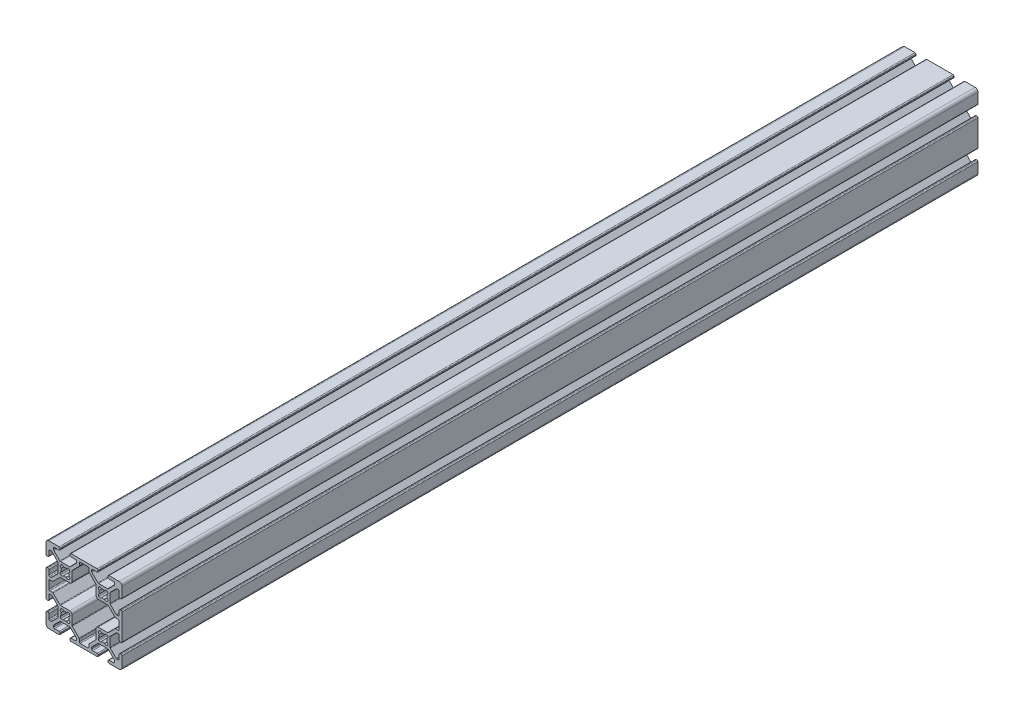
SolidWorks part; units mm, degrees
ref_plane "Front Plane" through (0, 0, 0) normal (0, 0, 1) x (1, 0, 0)
ref_plane "Top Plane" through (0, 0, 0) normal (0, 1, 0) x (1, 0, 0)
ref_plane "Right Plane" through (0, 0, 0) normal (1, 0, 0) x (0, 0, -1)
ref_plane "Plane1" through (0, 0, -450) normal (0, 0, -1) x (-1, 0, 0)
sketch "Sketch1" plane through (0, 0, -450) normal (0, 0, -1) x (-1, 0, 0)
  line L0 (18.5, 11.997) -> (18.5, 8.003)
  line L1 (17.992, 7.495) -> (16.6449, 7.495)
  line L2 (16.2857, 7.3462) -> (12.7433, 3.8038)
  line L3 (12.3841, 3.655) -> (7.488, 3.655)
  line L4 (6.345, 2.512) -> (6.345, -2.3838)
  line L5 (6.1962, -2.743) -> (2.6538, -6.2854)
  line L6 (2.505, -6.6446) -> (2.505, -7.992)
  line L7 (1.997, -8.5) -> (-1.997, -8.5)
  line L8 (-2.505, -7.992) -> (-2.505, -6.6446)
  line L9 (-2.6538, -6.2854) -> (-6.1962, -2.743)
  line L10 (-6.345, -2.3838) -> (-6.345, 2.512)
  line L11 (-7.488, 3.655) -> (-12.3841, 3.655)
  line L12 (-12.7433, 3.8038) -> (-16.2857, 7.3462)
  line L13 (-16.6449, 7.495) -> (-17.992, 7.495)
  line L14 (-18.5, 8.003) -> (-18.5, 11.997)
  line L15 (-17.992, 12.505) -> (-16.6449, 12.505)
  line L16 (-16.2857, 12.6538) -> (-12.7433, 16.1962)
  line L17 (-12.3841, 16.345) -> (-7.488, 16.345)
  line L18 (-6.345, 17.488) -> (-6.345, 22.3838)
  line L19 (-6.1962, 22.743) -> (-2.6538, 26.2854)
  line L20 (-2.505, 26.6446) -> (-2.505, 27.992)
  line L21 (-1.997, 28.5) -> (1.997, 28.5)
  line L22 (2.505, 27.992) -> (2.505, 26.6446)
  line L23 (2.6538, 26.2854) -> (6.1962, 22.743)
  line L24 (6.345, 22.3838) -> (6.345, 17.488)
  line L25 (7.488, 16.345) -> (12.3841, 16.345)
  line L26 (12.7433, 16.1962) -> (16.2857, 12.6538)
  line L27 (16.6449, 12.505) -> (17.992, 12.505)
  line L28 (12.1245, 22.3045) -> (12.3045, 22.1245)
  line L29 (12.3045, 17.8755) -> (12.1245, 17.6955)
  line L30 (7.8755, 17.6955) -> (7.6955, 17.8755)
  line L31 (7.6955, 22.1245) -> (7.8755, 22.3045)
  line L32 (12.3045, -2.1245) -> (12.1245, -2.3045)
  line L33 (7.8755, -2.3045) -> (7.6955, -2.1245)
  line L34 (7.6955, 2.1245) -> (7.8755, 2.3045)
  line L35 (12.1245, 2.3045) -> (12.3045, 2.1245)
  line L36 (-7.8755, 22.3045) -> (-7.6955, 22.1245)
  line L37 (-7.6955, 17.8755) -> (-7.8755, 17.6955)
  line L38 (-12.1245, 17.6955) -> (-12.3045, 17.8755)
  line L39 (-12.3045, 22.1245) -> (-12.1245, 22.3045)
  line L40 (-7.6955, -2.1245) -> (-7.8755, -2.3045)
  line L41 (-12.1245, -2.3045) -> (-12.3045, -2.1245)
  line L42 (-12.3045, 2.1245) -> (-12.1245, 2.3045)
  line L43 (-7.8755, 2.3045) -> (-7.6955, 2.1245)
  line L44 (18.5, 30) -> (13.138, 30)
  line L45 (12.63, 29.492) -> (12.63, 29.008)
  line L46 (13.138, 28.5) -> (15.487, 28.5)
  line L47 (15.995, 27.992) -> (15.995, 27.2662)
  line L48 (15.8462, 26.907) -> (12.743, 23.8038)
  line L49 (12.3838, 23.655) -> (7.6159, 23.655)
  line L50 (7.2567, 23.8038) -> (4.1538, 26.9067)
  line L51 (4.005, 27.2659) -> (4.005, 27.992)
  line L52 (4.513, 28.5) -> (6.862, 28.5)
  line L53 (7.37, 29.008) -> (7.37, 29.492)
  line L54 (6.862, 30) -> (-6.862, 30)
  line L55 (-7.37, 29.492) -> (-7.37, 29.008)
  line L56 (-6.862, 28.5) -> (-4.513, 28.5)
  line L57 (-4.005, 27.992) -> (-4.005, 27.2659)
  line L58 (-4.1538, 26.9067) -> (-7.2567, 23.8038)
  line L59 (-7.6159, 23.655) -> (-12.3838, 23.655)
  line L60 (-12.743, 23.8038) -> (-15.8462, 26.907)
  line L61 (-15.995, 27.2662) -> (-15.995, 27.992)
  line L62 (-15.487, 28.5) -> (-13.138, 28.5)
  line L63 (-12.63, 29.008) -> (-12.63, 29.492)
  line L64 (-13.138, 30) -> (-18.5, 30)
  line L65 (-20, 28.5) -> (-20, 23.138)
  line L66 (-19.492, 22.63) -> (-19.008, 22.63)
  line L67 (-18.5, 23.138) -> (-18.5, 25.487)
  line L68 (-17.992, 25.995) -> (-17.2659, 25.995)
  line L69 (-16.9067, 25.8462) -> (-13.8038, 22.7433)
  line L70 (-13.655, 22.3841) -> (-13.655, 17.6162)
  line L71 (-13.8038, 17.257) -> (-16.907, 14.1538)
  line L72 (-17.2662, 14.005) -> (-17.992, 14.005)
  line L73 (-18.5, 14.513) -> (-18.5, 16.862)
  line L74 (-19.008, 17.37) -> (-19.492, 17.37)
  line L75 (-20, 16.862) -> (-20, 3.138)
  line L76 (-19.492, 2.63) -> (-19.008, 2.63)
  line L77 (-18.5, 3.138) -> (-18.5, 5.487)
  line L78 (-17.992, 5.995) -> (-17.2662, 5.995)
  line L79 (-16.907, 5.8462) -> (-13.8038, 2.743)
  line L80 (-13.655, 2.3838) -> (-13.655, -2.3841)
  line L81 (-13.8038, -2.7433) -> (-16.9067, -5.8462)
  line L82 (-17.2659, -5.995) -> (-17.992, -5.995)
  line L83 (-18.5, -5.487) -> (-18.5, -3.138)
  line L84 (-19.008, -2.63) -> (-19.492, -2.63)
  line L85 (-20, -3.138) -> (-20, -8.5)
  line L86 (-18.5, -10) -> (-13.138, -10)
  line L87 (-12.63, -9.492) -> (-12.63, -9.008)
  line L88 (-13.138, -8.5) -> (-15.487, -8.5)
  line L89 (-15.995, -7.992) -> (-15.995, -7.2662)
  line L90 (-15.8462, -6.907) -> (-12.743, -3.8038)
  line L91 (-12.3838, -3.655) -> (-7.6159, -3.655)
  line L92 (-7.2567, -3.8038) -> (-4.1538, -6.9067)
  line L93 (-4.005, -7.2659) -> (-4.005, -7.992)
  line L94 (-4.513, -8.5) -> (-6.862, -8.5)
  line L95 (-7.37, -9.008) -> (-7.37, -9.492)
  line L96 (-6.862, -10) -> (6.862, -10)
  line L97 (7.37, -9.492) -> (7.37, -9.008)
  line L98 (6.862, -8.5) -> (4.513, -8.5)
  line L99 (4.005, -7.992) -> (4.005, -7.2659)
  line L100 (4.1538, -6.9067) -> (7.2567, -3.8038)
  line L101 (7.6159, -3.655) -> (12.3838, -3.655)
  line L102 (12.743, -3.8038) -> (15.8462, -6.907)
  line L103 (15.995, -7.2662) -> (15.995, -7.992)
  line L104 (15.487, -8.5) -> (13.138, -8.5)
  line L105 (12.63, -9.008) -> (12.63, -9.492)
  line L106 (13.138, -10) -> (18.5, -10)
  line L107 (20, -8.5) -> (20, -3.138)
  line L108 (19.492, -2.63) -> (19.008, -2.63)
  line L109 (18.5, -3.138) -> (18.5, -5.487)
  line L110 (17.992, -5.995) -> (17.2659, -5.995)
  line L111 (16.9067, -5.8462) -> (13.8038, -2.7433)
  line L112 (13.655, -2.3841) -> (13.655, 2.3838)
  line L113 (13.8038, 2.743) -> (16.907, 5.8462)
  line L114 (17.2662, 5.995) -> (17.992, 5.995)
  line L115 (18.5, 5.487) -> (18.5, 3.138)
  line L116 (19.008, 2.63) -> (19.492, 2.63)
  line L117 (20, 3.138) -> (20, 16.862)
  line L118 (19.492, 17.37) -> (19.008, 17.37)
  line L119 (18.5, 16.862) -> (18.5, 14.513)
  line L120 (17.992, 14.005) -> (17.2662, 14.005)
  line L121 (16.907, 14.1538) -> (13.8038, 17.257)
  line L122 (13.655, 17.6162) -> (13.655, 22.3841)
  line L123 (13.8038, 22.7433) -> (16.9067, 25.8462)
  line L124 (17.2659, 25.995) -> (17.992, 25.995)
  line L125 (18.5, 25.487) -> (18.5, 23.138)
  line L126 (19.008, 22.63) -> (19.492, 22.63)
  line L127 (20, 23.138) -> (20, 28.5)
  arc A0 (18.5, 8.003) -> (17.992, 7.495) centre (17.992, 8.003) cw
  arc A1 (16.6449, 7.495) -> (16.2857, 7.3462) centre (16.6449, 6.987) ccw
  arc A2 (12.7433, 3.8038) -> (12.3841, 3.655) centre (12.3841, 4.163) cw
  arc A3 (7.488, 3.655) -> (6.345, 2.512) centre (7.488, 2.512) ccw
  arc A4 (6.345, -2.3838) -> (6.1962, -2.743) centre (5.837, -2.3838) cw
  arc A5 (2.6538, -6.2854) -> (2.505, -6.6446) centre (3.013, -6.6446) ccw
  arc A6 (2.505, -7.992) -> (1.997, -8.5) centre (1.997, -7.992) cw
  arc A7 (-1.997, -8.5) -> (-2.505, -7.992) centre (-1.997, -7.992) cw
  arc A8 (-2.505, -6.6446) -> (-2.6538, -6.2854) centre (-3.013, -6.6446) ccw
  arc A9 (-6.1962, -2.743) -> (-6.345, -2.3838) centre (-5.837, -2.3838) cw
  arc A10 (-6.345, 2.512) -> (-7.488, 3.655) centre (-7.488, 2.512) ccw
  arc A11 (-12.3841, 3.655) -> (-12.7433, 3.8038) centre (-12.3841, 4.163) cw
  arc A12 (-16.2857, 7.3462) -> (-16.6449, 7.495) centre (-16.6449, 6.987) ccw
  arc A13 (-17.992, 7.495) -> (-18.5, 8.003) centre (-17.992, 8.003) cw
  arc A14 (-18.5, 11.997) -> (-17.992, 12.505) centre (-17.992, 11.997) cw
  arc A15 (-16.6449, 12.505) -> (-16.2857, 12.6538) centre (-16.6449, 13.013) ccw
  arc A16 (-12.7433, 16.1962) -> (-12.3841, 16.345) centre (-12.3841, 15.837) cw
  arc A17 (-7.488, 16.345) -> (-6.345, 17.488) centre (-7.488, 17.488) ccw
  arc A18 (-6.345, 22.3838) -> (-6.1962, 22.743) centre (-5.837, 22.3838) cw
  arc A19 (-2.6538, 26.2854) -> (-2.505, 26.6446) centre (-3.013, 26.6446) ccw
  arc A20 (-2.505, 27.992) -> (-1.997, 28.5) centre (-1.997, 27.992) cw
  arc A21 (1.997, 28.5) -> (2.505, 27.992) centre (1.997, 27.992) cw
  arc A22 (2.505, 26.6446) -> (2.6538, 26.2854) centre (3.013, 26.6446) ccw
  arc A23 (6.1962, 22.743) -> (6.345, 22.3838) centre (5.837, 22.3838) cw
  arc A24 (6.345, 17.488) -> (7.488, 16.345) centre (7.488, 17.488) ccw
  arc A25 (12.3841, 16.345) -> (12.7433, 16.1962) centre (12.3841, 15.837) cw
  arc A26 (16.2857, 12.6538) -> (16.6449, 12.505) centre (16.6449, 13.013) ccw
  arc A27 (17.992, 12.505) -> (18.5, 11.997) centre (17.992, 11.997) cw
  arc A28 (12.3045, 22.1245) -> (11.9358, 20.8037) centre (11.748, 21.568) cw
  arc A29 (11.9358, 20.8037) -> (11.9358, 19.1963) centre (10, 20) cw
  arc A30 (11.9358, 19.1963) -> (12.3045, 17.8755) centre (11.748, 18.432) cw
  arc A31 (12.1245, 17.6955) -> (10.8037, 18.0642) centre (11.568, 18.252) cw
  arc A32 (10.8037, 18.0642) -> (9.1963, 18.0642) centre (10, 20) cw
  arc A33 (9.1963, 18.0642) -> (7.8755, 17.6955) centre (8.432, 18.252) cw
  arc A34 (7.6955, 17.8755) -> (8.0642, 19.1963) centre (8.252, 18.432) cw
  arc A35 (8.0642, 19.1963) -> (8.0642, 20.8037) centre (10, 20) cw
  arc A36 (8.0642, 20.8037) -> (7.6955, 22.1245) centre (8.252, 21.568) cw
  arc A37 (7.8755, 22.3045) -> (9.1963, 21.9358) centre (8.432, 21.748) cw
  arc A38 (9.1963, 21.9358) -> (10.8037, 21.9358) centre (10, 20) cw
  arc A39 (10.8037, 21.9358) -> (12.1245, 22.3045) centre (11.568, 21.748) cw
  arc A40 (11.9358, 0.8037) -> (11.9358, -0.8037) centre (10, 0) cw
  arc A41 (11.9358, -0.8037) -> (12.3045, -2.1245) centre (11.748, -1.568) cw
  arc A42 (12.1245, -2.3045) -> (10.8037, -1.9358) centre (11.568, -1.748) cw
  arc A43 (10.8037, -1.9358) -> (9.1963, -1.9358) centre (10, 0) cw
  arc A44 (9.1963, -1.9358) -> (7.8755, -2.3045) centre (8.432, -1.748) cw
  arc A45 (7.6955, -2.1245) -> (8.0642, -0.8037) centre (8.252, -1.568) cw
  arc A46 (8.0642, -0.8037) -> (8.0642, 0.8037) centre (10, 0) cw
  arc A47 (8.0642, 0.8037) -> (7.6955, 2.1245) centre (8.252, 1.568) cw
  arc A48 (7.8755, 2.3045) -> (9.1963, 1.9358) centre (8.432, 1.748) cw
  arc A49 (9.1963, 1.9358) -> (10.8037, 1.9358) centre (10, 0) cw
  arc A50 (10.8037, 1.9358) -> (12.1245, 2.3045) centre (11.568, 1.748) cw
  arc A51 (12.3045, 2.1245) -> (11.9358, 0.8037) centre (11.748, 1.568) cw
  arc A52 (-7.6955, 22.1245) -> (-8.0642, 20.8037) centre (-8.252, 21.568) cw
  arc A53 (-8.0642, 20.8037) -> (-8.0642, 19.1963) centre (-10, 20) cw
  arc A54 (-8.0642, 19.1963) -> (-7.6955, 17.8755) centre (-8.252, 18.432) cw
  arc A55 (-7.8755, 17.6955) -> (-9.1963, 18.0642) centre (-8.432, 18.252) cw
  arc A56 (-9.1963, 18.0642) -> (-10.8037, 18.0642) centre (-10, 20) cw
  arc A57 (-10.8037, 18.0642) -> (-12.1245, 17.6955) centre (-11.568, 18.252) cw
  arc A58 (-12.3045, 17.8755) -> (-11.9358, 19.1963) centre (-11.748, 18.432) cw
  arc A59 (-11.9358, 19.1963) -> (-11.9358, 20.8037) centre (-10, 20) cw
  arc A60 (-11.9358, 20.8037) -> (-12.3045, 22.1245) centre (-11.748, 21.568) cw
  arc A61 (-12.1245, 22.3045) -> (-10.8037, 21.9358) centre (-11.568, 21.748) cw
  arc A62 (-10.8037, 21.9358) -> (-9.1963, 21.9358) centre (-10, 20) cw
  arc A63 (-9.1963, 21.9358) -> (-7.8755, 22.3045) centre (-8.432, 21.748) cw
  arc A64 (-8.0642, 0.8037) -> (-8.0642, -0.8037) centre (-10, 0) cw
  arc A65 (-8.0642, -0.8037) -> (-7.6955, -2.1245) centre (-8.252, -1.568) cw
  arc A66 (-7.8755, -2.3045) -> (-9.1963, -1.9358) centre (-8.432, -1.748) cw
  arc A67 (-9.1963, -1.9358) -> (-10.8037, -1.9358) centre (-10, 0) cw
  arc A68 (-10.8037, -1.9358) -> (-12.1245, -2.3045) centre (-11.568, -1.748) cw
  arc A69 (-12.3045, -2.1245) -> (-11.9358, -0.8037) centre (-11.748, -1.568) cw
  arc A70 (-11.9358, -0.8037) -> (-11.9358, 0.8037) centre (-10, 0) cw
  arc A71 (-11.9358, 0.8037) -> (-12.3045, 2.1245) centre (-11.748, 1.568) cw
  arc A72 (-12.1245, 2.3045) -> (-10.8037, 1.9358) centre (-11.568, 1.748) cw
  arc A73 (-10.8037, 1.9358) -> (-9.1963, 1.9358) centre (-10, 0) cw
  arc A74 (-9.1963, 1.9358) -> (-7.8755, 2.3045) centre (-8.432, 1.748) cw
  arc A75 (-7.6955, 2.1245) -> (-8.0642, 0.8037) centre (-8.252, 1.568) cw
  arc A76 (20, 28.5) -> (18.5, 30) centre (18.5, 28.5) ccw
  arc A77 (13.138, 30) -> (12.63, 29.492) centre (13.138, 29.492) ccw
  arc A78 (12.63, 29.008) -> (13.138, 28.5) centre (13.138, 29.008) ccw
  arc A79 (15.487, 28.5) -> (15.995, 27.992) centre (15.487, 27.992) cw
  arc A80 (15.995, 27.2662) -> (15.8462, 26.907) centre (15.487, 27.2662) cw
  arc A81 (12.743, 23.8038) -> (12.3838, 23.655) centre (12.3838, 24.163) cw
  arc A82 (7.6159, 23.655) -> (7.2567, 23.8038) centre (7.6159, 24.163) cw
  arc A83 (4.1538, 26.9067) -> (4.005, 27.2659) centre (4.513, 27.2659) cw
  arc A84 (4.005, 27.992) -> (4.513, 28.5) centre (4.513, 27.992) cw
  arc A85 (6.862, 28.5) -> (7.37, 29.008) centre (6.862, 29.008) ccw
  arc A86 (7.37, 29.492) -> (6.862, 30) centre (6.862, 29.492) ccw
  arc A87 (-6.862, 30) -> (-7.37, 29.492) centre (-6.862, 29.492) ccw
  arc A88 (-7.37, 29.008) -> (-6.862, 28.5) centre (-6.862, 29.008) ccw
  arc A89 (-4.513, 28.5) -> (-4.005, 27.992) centre (-4.513, 27.992) cw
  arc A90 (-4.005, 27.2659) -> (-4.1538, 26.9067) centre (-4.513, 27.2659) cw
  arc A91 (-7.2567, 23.8038) -> (-7.6159, 23.655) centre (-7.6159, 24.163) cw
  arc A92 (-12.3838, 23.655) -> (-12.743, 23.8038) centre (-12.3838, 24.163) cw
  arc A93 (-15.8462, 26.907) -> (-15.995, 27.2662) centre (-15.487, 27.2662) cw
  arc A94 (-15.995, 27.992) -> (-15.487, 28.5) centre (-15.487, 27.992) cw
  arc A95 (-13.138, 28.5) -> (-12.63, 29.008) centre (-13.138, 29.008) ccw
  arc A96 (-12.63, 29.492) -> (-13.138, 30) centre (-13.138, 29.492) ccw
  arc A97 (-18.5, 30) -> (-20, 28.5) centre (-18.5, 28.5) ccw
  arc A98 (-20, 23.138) -> (-19.492, 22.63) centre (-19.492, 23.138) ccw
  arc A99 (-19.008, 22.63) -> (-18.5, 23.138) centre (-19.008, 23.138) ccw
  arc A100 (-18.5, 25.487) -> (-17.992, 25.995) centre (-17.992, 25.487) cw
  arc A101 (-17.2659, 25.995) -> (-16.9067, 25.8462) centre (-17.2659, 25.487) cw
  arc A102 (-13.8038, 22.7433) -> (-13.655, 22.3841) centre (-14.163, 22.3841) cw
  arc A103 (-13.655, 17.6162) -> (-13.8038, 17.257) centre (-14.163, 17.6162) cw
  arc A104 (-16.907, 14.1538) -> (-17.2662, 14.005) centre (-17.2662, 14.513) cw
  arc A105 (-17.992, 14.005) -> (-18.5, 14.513) centre (-17.992, 14.513) cw
  arc A106 (-18.5, 16.862) -> (-19.008, 17.37) centre (-19.008, 16.862) ccw
  arc A107 (-19.492, 17.37) -> (-20, 16.862) centre (-19.492, 16.862) ccw
  arc A108 (-20, 3.138) -> (-19.492, 2.63) centre (-19.492, 3.138) ccw
  arc A109 (-19.008, 2.63) -> (-18.5, 3.138) centre (-19.008, 3.138) ccw
  arc A110 (-18.5, 5.487) -> (-17.992, 5.995) centre (-17.992, 5.487) cw
  arc A111 (-17.2662, 5.995) -> (-16.907, 5.8462) centre (-17.2662, 5.487) cw
  arc A112 (-13.8038, 2.743) -> (-13.655, 2.3838) centre (-14.163, 2.3838) cw
  arc A113 (-13.655, -2.3841) -> (-13.8038, -2.7433) centre (-14.163, -2.3841) cw
  arc A114 (-16.9067, -5.8462) -> (-17.2659, -5.995) centre (-17.2659, -5.487) cw
  arc A115 (-17.992, -5.995) -> (-18.5, -5.487) centre (-17.992, -5.487) cw
  arc A116 (-18.5, -3.138) -> (-19.008, -2.63) centre (-19.008, -3.138) ccw
  arc A117 (-19.492, -2.63) -> (-20, -3.138) centre (-19.492, -3.138) ccw
  arc A118 (-20, -8.5) -> (-18.5, -10) centre (-18.5, -8.5) ccw
  arc A119 (-13.138, -10) -> (-12.63, -9.492) centre (-13.138, -9.492) ccw
  arc A120 (-12.63, -9.008) -> (-13.138, -8.5) centre (-13.138, -9.008) ccw
  arc A121 (-15.487, -8.5) -> (-15.995, -7.992) centre (-15.487, -7.992) cw
  arc A122 (-15.995, -7.2662) -> (-15.8462, -6.907) centre (-15.487, -7.2662) cw
  arc A123 (-12.743, -3.8038) -> (-12.3838, -3.655) centre (-12.3838, -4.163) cw
  arc A124 (-7.6159, -3.655) -> (-7.2567, -3.8038) centre (-7.6159, -4.163) cw
  arc A125 (-4.1538, -6.9067) -> (-4.005, -7.2659) centre (-4.513, -7.2659) cw
  arc A126 (-4.005, -7.992) -> (-4.513, -8.5) centre (-4.513, -7.992) cw
  arc A127 (-6.862, -8.5) -> (-7.37, -9.008) centre (-6.862, -9.008) ccw
  arc A128 (-7.37, -9.492) -> (-6.862, -10) centre (-6.862, -9.492) ccw
  arc A129 (6.862, -10) -> (7.37, -9.492) centre (6.862, -9.492) ccw
  arc A130 (7.37, -9.008) -> (6.862, -8.5) centre (6.862, -9.008) ccw
  arc A131 (4.513, -8.5) -> (4.005, -7.992) centre (4.513, -7.992) cw
  arc A132 (4.005, -7.2659) -> (4.1538, -6.9067) centre (4.513, -7.2659) cw
  arc A133 (7.2567, -3.8038) -> (7.6159, -3.655) centre (7.6159, -4.163) cw
  arc A134 (12.3838, -3.655) -> (12.743, -3.8038) centre (12.3838, -4.163) cw
  arc A135 (15.8462, -6.907) -> (15.995, -7.2662) centre (15.487, -7.2662) cw
  arc A136 (15.995, -7.992) -> (15.487, -8.5) centre (15.487, -7.992) cw
  arc A137 (13.138, -8.5) -> (12.63, -9.008) centre (13.138, -9.008) ccw
  arc A138 (12.63, -9.492) -> (13.138, -10) centre (13.138, -9.492) ccw
  arc A139 (18.5, -10) -> (20, -8.5) centre (18.5, -8.5) ccw
  arc A140 (20, -3.138) -> (19.492, -2.63) centre (19.492, -3.138) ccw
  arc A141 (19.008, -2.63) -> (18.5, -3.138) centre (19.008, -3.138) ccw
  arc A142 (18.5, -5.487) -> (17.992, -5.995) centre (17.992, -5.487) cw
  arc A143 (17.2659, -5.995) -> (16.9067, -5.8462) centre (17.2659, -5.487) cw
  arc A144 (13.8038, -2.7433) -> (13.655, -2.3841) centre (14.163, -2.3841) cw
  arc A145 (13.655, 2.3838) -> (13.8038, 2.743) centre (14.163, 2.3838) cw
  arc A146 (16.907, 5.8462) -> (17.2662, 5.995) centre (17.2662, 5.487) cw
  arc A147 (17.992, 5.995) -> (18.5, 5.487) centre (17.992, 5.487) cw
  arc A148 (18.5, 3.138) -> (19.008, 2.63) centre (19.008, 3.138) ccw
  arc A149 (19.492, 2.63) -> (20, 3.138) centre (19.492, 3.138) ccw
  arc A150 (20, 16.862) -> (19.492, 17.37) centre (19.492, 16.862) ccw
  arc A151 (19.008, 17.37) -> (18.5, 16.862) centre (19.008, 16.862) ccw
  arc A152 (18.5, 14.513) -> (17.992, 14.005) centre (17.992, 14.513) cw
  arc A153 (17.2662, 14.005) -> (16.907, 14.1538) centre (17.2662, 14.513) cw
  arc A154 (13.8038, 17.257) -> (13.655, 17.6162) centre (14.163, 17.6162) cw
  arc A155 (13.655, 22.3841) -> (13.8038, 22.7433) centre (14.163, 22.3841) cw
  arc A156 (16.9067, 25.8462) -> (17.2659, 25.995) centre (17.2659, 25.487) cw
  arc A157 (17.992, 25.995) -> (18.5, 25.487) centre (17.992, 25.487) cw
  arc A158 (18.5, 23.138) -> (19.008, 22.63) centre (19.008, 23.138) ccw
  arc A159 (19.492, 22.63) -> (20, 23.138) centre (19.492, 23.138) ccw
extrude "Boss-Extrude1" add sketch "Sketch1" against normal blind 450
